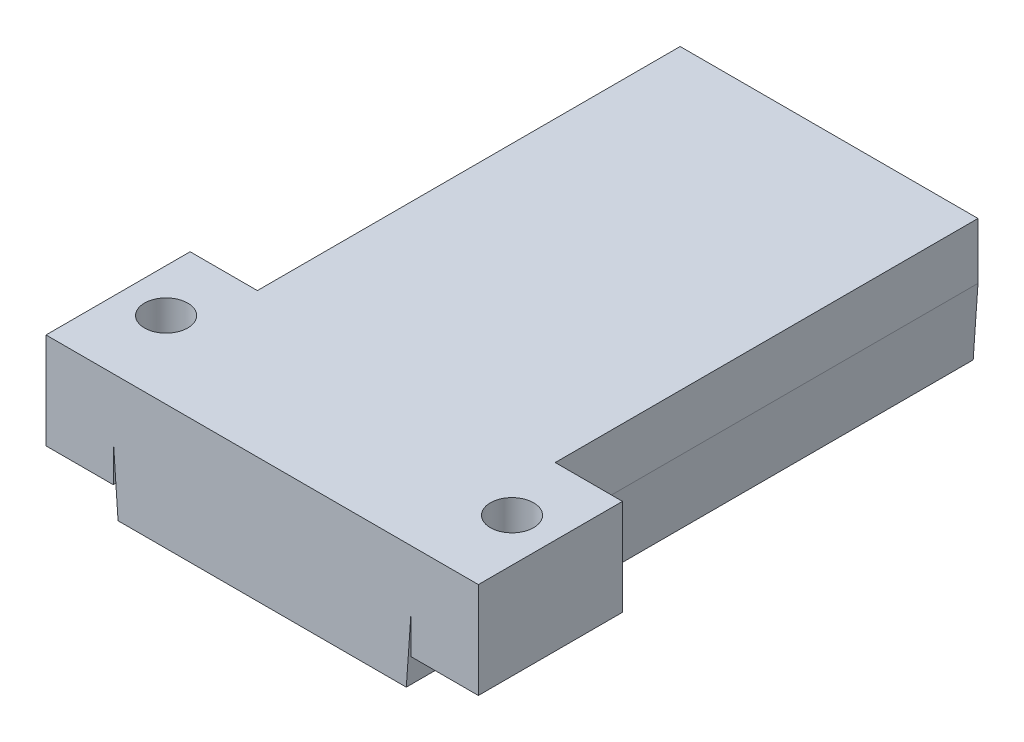
SolidWorks part; units mm, degrees
ref_plane "Front Plane" through (0, 0, 0) normal (0, 0, 1) x (1, 0, 0)
ref_plane "Top Plane" through (0, 0, 0) normal (0, 1, 0) x (1, 0, 0)
ref_plane "Right Plane" through (0, 0, 0) normal (1, 0, 0) x (0, 0, -1)
sketch "Sketch1" plane through (0, 0, 0) normal (0, 1, 0) x (1, 0, 0)
  line L0 (-23, 32) -> (-23, 22)
  line L1 (0, 0) -> (-26, 0)
  line L2 (0, 0) -> (0, 53)
  line L3 (0, 53) -> (-26, 53)
  line L4 (-26, 0) -> (-26, 53)
  line L5 (-23, 48) -> (-3, 48)
  line L6 (-23, 48) -> (-23, 38)
  line L7 (-23, 38) -> (-3, 38)
  line L8 (-3, 48) -> (-3, 38)
  line L9 (-23, 32) -> (-3, 32)
  line L10 (-3, 32) -> (-3, 22)
  line L11 (-23, 22) -> (-3, 22)
  line L12 (-23, 16) -> (-23, 6)
  line L13 (-23, 16) -> (-3, 16)
  line L14 (-3, 16) -> (-3, 6)
  line L15 (-23, 6) -> (-3, 6)
  point P9 (-13, 48)
  point P10 (-13, 53)
  dimension "D1" = 26
  dimension "D2" = 53
  dimension "D3" = 20
  dimension "D4" = 10
  dimension "D5" = 5
  dimension "D6" = 3
extrude "Boss-Extrude1" add sketch "Sketch1" along normal blind 5
sketch "Sketch2" plane through (0, 5, 0) normal (0, 1, 0) x (1, 0, 0)
  line L17 (-26, 53) -> (0, 53)
  line L18 (-26, 53) -> (-26, 0)
  line L19 (-26, 0) -> (0, 0)
  line L20 (0, 53) -> (0, 0)
  line L21 (-28.5, 56) -> (2.5, 56)
  line L22 (-28.5, 56) -> (-28.5, -3)
  line L23 (-28.5, -3) -> (2.5, -3)
  line L24 (2.5, 56) -> (2.5, -3)
  dimension "D1" = 3
  dimension "D2" = 2.5
  dimension "D3" = 2.5
  dimension "D4" = 3
extrude "Boss-Extrude2" add sketch "Sketch2" against normal blind 10
sketch "Sketch3" plane through (0, 5, 0) normal (0, 1, 0) x (1, 0, 0)
  line L1 (-28.5, 56) -> (2.5, 56)
  line L2 (-28.5, 56) -> (-28.5, -3)
  line L3 (-28.5, -3) -> (2.5, -3)
  line L4 (2.5, 56) -> (2.5, -3)
extrude "Boss-Extrude3" add sketch "Sketch3" along normal blind 3
sketch "Sketch4" plane through (0, 8, 0) normal (0, 1, 0) x (1, 0, 0)
  line L1 (-5, 56) -> (-11, 56)
  line L2 (-5, 56) -> (-5, 10)
  line L3 (-5, 10) -> (-11, 10)
  line L4 (-11, 56) -> (-11, 10)
  line L6 (-3, 38) -> (-3, 48) construction
  line L8 (-28.5, -3) -> (2.5, -3) construction
  dimension "D1" = 6
  dimension "D2" = 2
  dimension "D3" = 46
  dimension "D4" = 13
extrude "Boss-Extrude4" [suppressed] add sketch "Sketch4" along normal blind 55
sketch "Sketch5" [suppressed] plane through (-5, 0, 0) normal (1, 0, 0) x (0, 0, -1)
  line L0 (10, 8) -> (56, 8) construction
  line L1 (56, 63) -> (56, 8) construction
  line L2 (19, 48) -> (50, 17) construction
  line L3 (50, 48) -> (19, 17) construction
  circle A0 centre (50, 17) radius 1.75
  circle A1 centre (19, 17) radius 1.75
  circle A2 centre (19, 48) radius 1.75
  circle A3 centre (50, 48) radius 1.75
  circle A4 centre (34.5, 32.5) radius 13.5
  dimension "D2" = 6
  dimension "D3" = 3.5
  dimension "D6" = 27
  dimension "D1" = 9
  dimension "D4" = 2
  dimension "D5" = 2
extrude "Cut-Extrude1" [suppressed] cut sketch "Sketch5" against normal through all
chamfer "Chamfer1" distance 0.5 angle 86 2 edges at (2.5, -5, -26.5) (-28.5, -5, -26.5)
sketch "Sketch6" [suppressed] plane through (-5, 0, 0) normal (1, 0, 0) x (0, 0, -1)
  line L0 (10, 63) -> (10, 8) construction
  line L1 (56, 63) -> (10, 63)
  line L2 (56, 63) -> (56, 56)
  line L3 (56, 56) -> (10, 56)
  line L4 (10, 63) -> (10, 56)
  dimension "D1" = 7
extrude "Boss-Extrude5" [suppressed] add sketch "Sketch6" along normal blind 14
sketch "Sketch7" [suppressed] plane through (0, 63, 0) normal (0, 1, 0) x (1, 0, 0)
  line L0 (-11, 56) -> (-11, 10) construction
  line L1 (-8.5, 39.5) -> (-3.5, 39.5)
  line L2 (-8.5, 39.5) -> (-8.5, 34.5)
  line L3 (-8.5, 34.5) -> (-3.5, 34.5)
  line L4 (-3.5, 39.5) -> (-3.5, 34.5)
  line L5 (1.5, 39.5) -> (6.5, 39.5)
  line L6 (1.5, 39.5) -> (1.5, 34.5)
  line L7 (1.5, 34.5) -> (6.5, 34.5)
  line L8 (6.5, 39.5) -> (6.5, 34.5)
  line L9 (-8.5, 16.5) -> (-3.5, 16.5)
  line L10 (-8.5, 16.5) -> (-8.5, 11.5)
  line L11 (-8.5, 11.5) -> (-3.5, 11.5)
  line L12 (-3.5, 16.5) -> (-3.5, 11.5)
  line L13 (1.5, 16.5) -> (6.5, 16.5)
  line L14 (1.5, 16.5) -> (1.5, 11.5)
  line L15 (1.5, 11.5) -> (6.5, 11.5)
  line L16 (6.5, 16.5) -> (6.5, 11.5)
  line L17 (-11, 10) -> (9, 10) construction
  point P18 (-6, 16.5)
  point P19 (-6, 39.5)
  point P20 (4, 39.5)
  point P21 (4, 16.5)
  point P22 (-3.5, 37)
  point P23 (1.5, 37)
  point P24 (-3.5, 14)
  point P25 (1.5, 14)
  dimension "D1" = 5
  dimension "D2" = 5
  dimension "D3" = 2.5
  dimension "D4" = 1.5
  dimension "D5" = 23
extrude "Cut-Extrude2" [suppressed] cut sketch "Sketch7" against normal blind 5
sketch "Sketch8" [suppressed] plane through (0, 0, -56) normal (0, 0, -1) x (-1, 0, 0)
  line L0 (-9, 56) -> (-9, 63) construction
  line L1 (-9, 8) -> (5.6893, 8)
  line L2 (-9, 8) -> (-9, 1)
  line L3 (-9, 1) -> (5.6893, 1)
  line L4 (5.6893, 8) -> (5.6893, 1)
  line L5 (-2.5, 8) -> (5, 8) construction
extrude "Boss-Extrude6" [suppressed] add sketch "Sketch8" against normal blind 7.5
sketch "Sketch9" [suppressed] plane through (0, 0, -56) normal (0, 0, -1) x (-1, 0, 0)
  line L0 (-9, 56) -> (-9, 63) construction
  line L1 (-9, 8) -> (-9, 1) construction
  line L2 (11, 63) -> (11, 8) construction
  line L3 (5, 56) -> (5, 8) construction
  line L4 (-9, 8) -> (5, 8) construction
  line L6 (-9, 56) -> (5, 56) construction
  circle A0 centre (-5.5, 59.5) radius 1.75
  circle A1 centre (-5.5, 4.5) radius 1.75
  circle A2 centre (8, 54) radius 1.75
  circle A3 centre (8, 10) radius 1.75
  circle A4 centre (8, 32) radius 1.75
  point P5 (-9, 59.5)
  point P9 (-9, 4.5)
  dimension "D1" = 3.5
  dimension "D2" = 3.5
  dimension "D3" = 3.5
  dimension "D4" = 3.5
  dimension "D5" = 3
  dimension "D6" = 3
  dimension "D7" = 3
  dimension "D8" = 2
  dimension "D9" = 2
  dimension "D10" = 22
  dimension "D11" = 22
extrude "Cut-Extrude3" [suppressed] cut sketch "Sketch9" against normal blind 4
sketch "Sketch10" plane through (0, 8, 0) normal (0, 1, 0) x (1, 0, 0)
  line L0 (-13, -3) -> (-13, 56) construction
  line L1 (2.5, -3) -> (9.5, -3)
  line L2 (2.5, -3) -> (2.5, 12)
  line L3 (2.5, 12) -> (9.5, 12)
  line L4 (9.5, -3) -> (9.5, 12)
  line L9 (-28.5, -3) -> (2.5, -3) construction
  line L10 (2.5, 56) -> (-28.5, 56) construction
  line L11 (-28.5, 12) -> (-35.5, 12)
  line L12 (-35.5, -3) -> (-35.5, 12)
  line L13 (-28.5, -3) -> (-35.5, -3)
  line L14 (-28.5, -3) -> (-28.5, 12)
  circle A0 centre (5, 5) radius 2.25
  circle A1 centre (-31, 5) radius 2.25
  dimension "D6" = 4.5
  dimension "D3" = 4.5
  dimension "D1" = 15
  dimension "D2" = 7
  dimension "D5" = 8
extrude "Boss-Extrude7" add sketch "Sketch10" against normal blind 10
